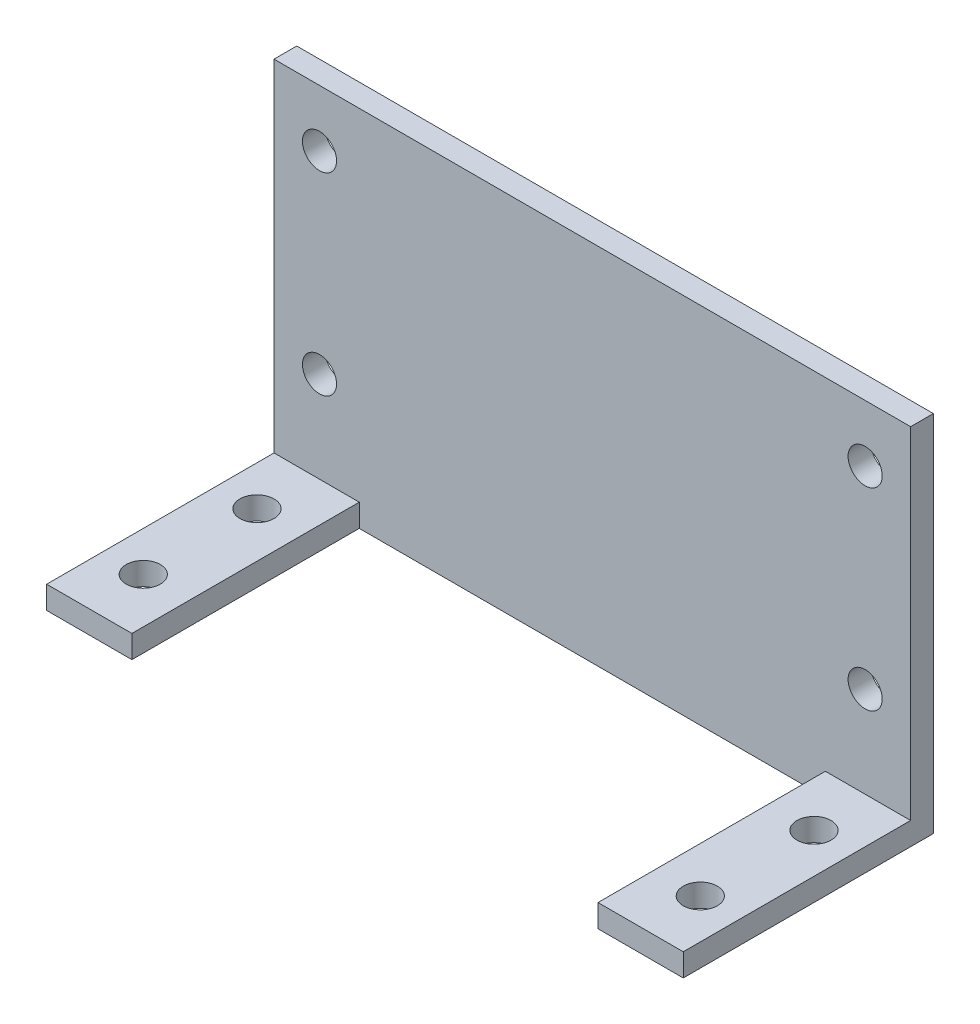
SolidWorks part; units mm, degrees
ref_plane "Plan de face" through (0, 0, 0) normal (0, 0, 1) x (1, 0, 0)
ref_plane "Plan de dessus" through (0, 0, 0) normal (0, 1, 0) x (1, 0, 0)
ref_plane "Plan de droite" through (0, 0, 0) normal (1, 0, 0) x (0, 0, -1)
sketch "Esquisse1" plane through (0, 0, 0) normal (0, 1, 0) x (1, 0, 0)
  line L1 (-28, 11) -> (28, 11)
  line L2 (-28, 11) -> (-28, -11)
  line L3 (-28, -11) -> (28, -11)
  line L4 (28, 11) -> (28, -11)
  dimension "D1" = 56
  dimension "D2" = 22
  dimension "D3" = 11
  dimension "D4" = 28
extrude "Boss.-Extru.1" add sketch "Esquisse1" along normal blind 2
sketch "Esquisse2" plane through (0, 2, 0) normal (0, 1, 0) x (1, 0, 0)
  line L0 (28, -11) -> (28, 11) construction
  line L1 (-28, 11) -> (28, 11)
  line L2 (-28, 11) -> (-28, 9)
  line L3 (-28, 9) -> (28, 9)
  line L4 (28, 11) -> (28, 9)
  dimension "D1" = 2
extrude "Boss.-Extru.2" add sketch "Esquisse2" along normal blind 30
sketch "Esquisse3" plane through (0, 2, 0) normal (0, 1, 0) x (1, 0, 0)
  line L0 (-28, -11) -> (28, -11) construction
  line L1 (-20.5, 9) -> (20.5, 9)
  line L2 (-20.5, 9) -> (-20.5, -11)
  line L3 (-20.5, -11) -> (20.5, -11)
  line L4 (20.5, 9) -> (20.5, -11)
  dimension "D1" = 0
  dimension "D2" = 41
  dimension "D3" = 20.5
  dimension "D4" = 20
extrude "Enlèv. mat.-Extru.1" cut sketch "Esquisse3" against normal blind 20
sketch "Esquisse5" plane through (0, 2, 0) normal (0, 1, 0) x (1, 0, 0)
  line L0 (20.5, -11) -> (20.5, 9) construction
  line L2 (-28, 9) -> (-20.5, 9) construction
  line L3 (-28, 9) -> (28, 9) construction
  circle A0 centre (-24.5, 4) radius 1.5
  circle A1 centre (-24.5, -6) radius 1.5
  circle A2 centre (24.5, 4) radius 1.5
  circle A3 centre (24.5, -6) radius 1.5
  dimension "D1" = 3
  dimension "D2" = 3
  dimension "D3" = 3
  dimension "D4" = 3
  dimension "D5" = 49
  dimension "D6" = 49
  dimension "D7" = 10
  dimension "D8" = 10
  dimension "D9" = 4
  dimension "D10" = 4
  dimension "D11" = 5
  dimension "D12" = 5
extrude "Enlèv. mat.-Extru.2" cut sketch "Esquisse5" against normal blind 20
sketch "Esquisse6" plane through (0, 0, -11) normal (0, 0, -1) x (-1, 0, 0)
  line L0 (28, 32) -> (28, 0) construction
  line L1 (-28, 32) -> (-28, 0) construction
  line L2 (-28, 32) -> (28, 32) construction
  line L3 (-28, 0) -> (28, 0) construction
  circle A0 centre (-24, 27) radius 1.5
  circle A1 centre (-24, 10) radius 1.5
  circle A2 centre (24, 10) radius 1.5
  circle A3 centre (24, 27) radius 1.5
  dimension "D1" = 3
  dimension "D2" = 3
  dimension "D3" = 3
  dimension "D4" = 3
  dimension "D5" = 4
  dimension "D6" = 4
  dimension "D7" = 4
  dimension "D8" = 4
  dimension "D9" = 5
  dimension "D10" = 5
  dimension "D11" = 10
  dimension "D12" = 10
extrude "Enlèv. mat.-Extru.3" cut sketch "Esquisse6" against normal blind 20
